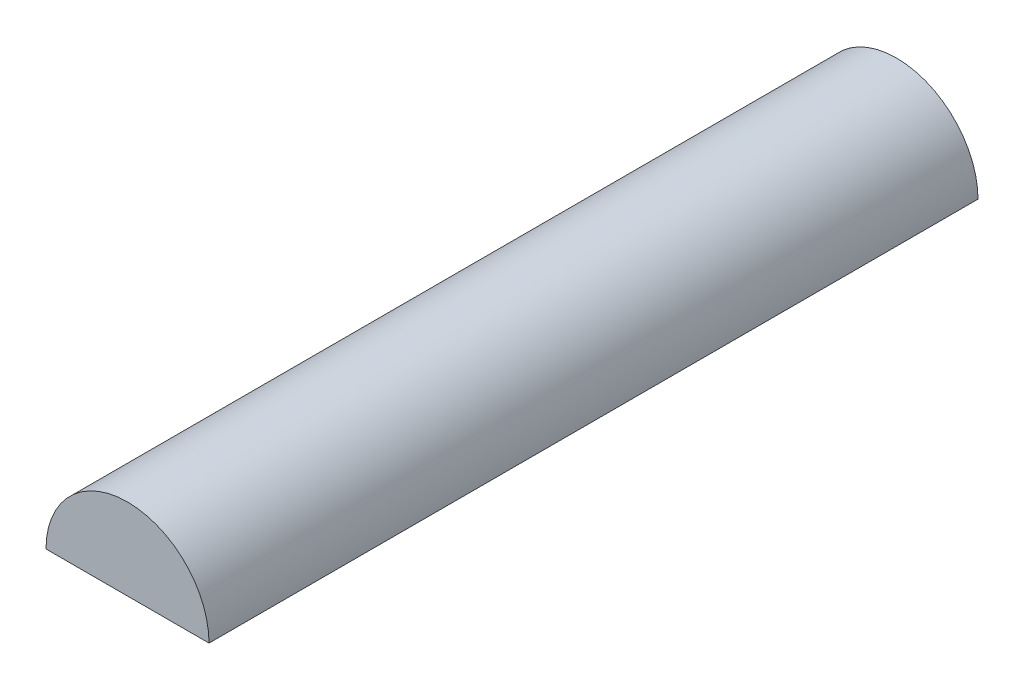
SolidWorks part; units mm, degrees
ref_plane "Front Plane" through (0, 0, 0) normal (0, 0, 1) x (1, 0, 0)
ref_plane "Top Plane" through (0, 0, 0) normal (0, 1, 0) x (1, 0, 0)
ref_plane "Right Plane" through (0, 0, 0) normal (1, 0, 0) x (0, 0, -1)
sketch "Sketch1" plane through (0, 0, 0) normal (0, 0, 1) x (1, 0, 0)
  line L0 (-2.65, 0) -> (2.65, 0)
  arc A0 (2.65, 0) -> (-2.65, 0) centre (0, 0) ccw
  dimension "D1" = 5.3
extrude "Boss-Extrude1" add sketch "Sketch1" along normal blind 25
